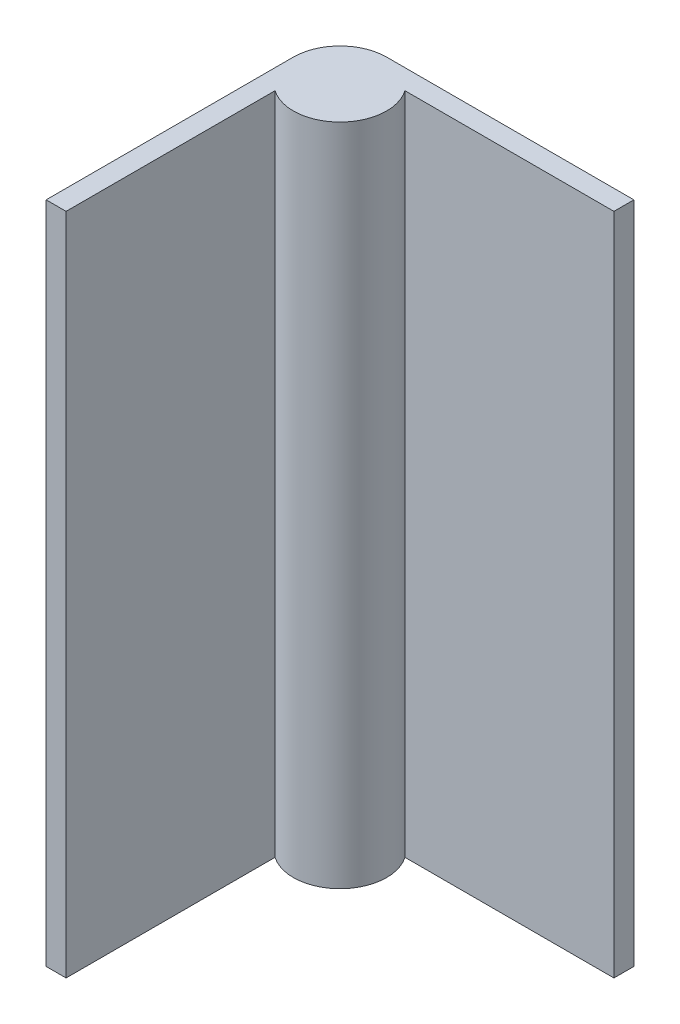
SolidWorks part; units mm, degrees
ref_plane "Front Plane" through (0, 0, 0) normal (0, 0, 1) x (1, 0, 0)
ref_plane "Top Plane" through (0, 0, 0) normal (0, 1, 0) x (1, 0, 0)
ref_plane "Right Plane" through (0, 0, 0) normal (1, 0, 0) x (0, 0, -1)
sketch "Sketch3" plane through (0, 0, 0) normal (0, 1, 0) x (1, 0, 0)
  line L0 (-7.47, 3.87) -> (-7.47, 5.67)
  line L1 (-3.87, 6.7) -> (3.87, 6.7)
  line L2 (-3.87, 6.7) -> (-3.87, 7.47) construction
  line L3 (-3.87, 7.47) -> (3.87, 7.47)
  line L4 (3.87, 6.7) -> (3.87, 7.47)
  line L5 (-6.7, 3.87) -> (-7.47, 3.87) construction
  line L6 (-6.7, 3.87) -> (-6.7, -3.87)
  line L7 (-6.7, -3.87) -> (-7.47, -3.87)
  line L8 (-7.47, 3.87) -> (-7.47, -3.87)
  line L9 (-6.7, 3.87) -> (-6.7, 4.1938)
  line L10 (-3.87, 7.47) -> (-5.67, 7.47)
  line L11 (-3.87, 6.7) -> (-4.1938, 6.7)
  circle A0 centre (-5.67, 5.67) radius 1.8 construction
  arc A1 (-7.47, 5.67) -> (-5.67, 7.47) centre (-5.67, 5.67) cw
  arc A2 (-4.1938, 6.7) -> (-6.7, 4.1938) centre (-5.67, 5.67) cw
  point P10 (-5.67, 3.87)
  point P11 (-3.87, 5.67)
  point P12 (-7.47, 5.67)
  point P13 (-5.67, 7.47)
  point P20 (0, 6.7)
  point P22 (-6.7, 0)
  dimension "D1" = 3.6
  dimension "D2" = 0.77
  dimension "D3" = 7.74
extrude "Boss-Extrude2" add sketch "Sketch3" along normal blind 25.62 contours A2 L11 L1 L4 L3 L10 A1 L0 L8 L7 L6 L9
